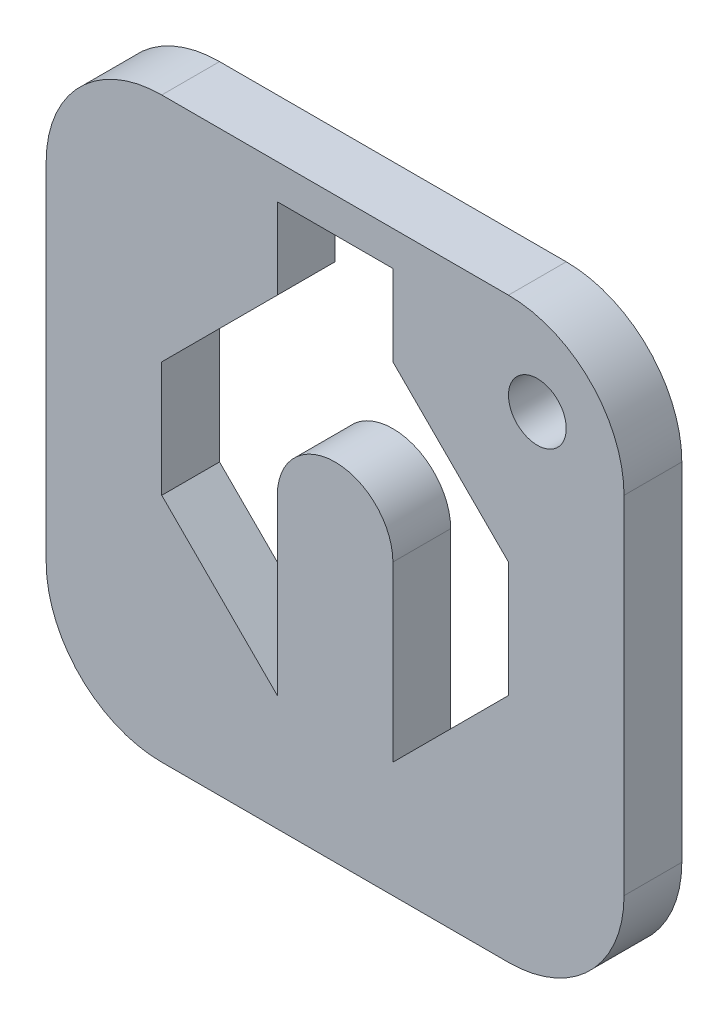
SolidWorks part; units mm, degrees
ref_plane "Z Plane" through (0, 0, 0) normal (0, 0, 1) x (1, 0, 0)
ref_plane "Y Plane" through (0, 0, 0) normal (0, 1, 0) x (1, 0, 0)
ref_plane "X Plane" through (0, 0, 0) normal (1, 0, 0) x (0, 0, -1)
sketch "Sketch2" plane through (0, 0, 0) normal (0, 0, 1) x (1, 0, 0)
  line L1 (-25, 25) -> (25, 25)
  line L2 (-25, 25) -> (-25, -25)
  line L3 (-25, -25) -> (25, -25)
  line L4 (25, 25) -> (25, -25)
  dimension "D1" = 50
  dimension "D2" = 50
  dimension "D3" = 25
  dimension "D4" = 25
extrude "Boss-Extrude1" add sketch "Sketch2" along normal blind 5
fillet "Fillet1" radius 10 4 edges at (-25, -25, 2.5) (25, 25, 2.5) (25, -25, 2.5) (-25, 25, 2.5)
sketch "Sketch3" plane through (0, 0, 5) normal (0, 0, 1) x (1, 0, 0)
  line L0 (-5, 0) -> (-5, -15)
  line L1 (-5, -15) -> (-15, -5)
  line L2 (-15, -5) -> (-15, 5)
  line L3 (-15, 5) -> (-5, 15)
  line L4 (-5, 15) -> (-5, 22)
  line L5 (-5, 22) -> (5, 22)
  line L6 (5, 22) -> (5, 15)
  line L7 (5, 15) -> (15, 5)
  line L8 (15, 5) -> (15, -5)
  line L9 (15, -5) -> (5, -15)
  line L10 (5, -15) -> (5, 0)
  line L11 (15, 25) -> (-15, 25) construction
  line L12 (-25, 15) -> (-25, -15) construction
  line L13 (25, -15) -> (25, 15) construction
  line L14 (-15, -25) -> (15, -25) construction
  circle A0 centre (17.5, 17.5) radius 2.5
  arc A2 (-5, 0) -> (5, 0) centre (0, 0) cw
  dimension "D1" = 5
  dimension "D2" = 3
  dimension "D3" = 10
  dimension "D4" = 10
  dimension "D5" = 10
  dimension "D6" = 10
  dimension "D7" = 45
  dimension "D8" = 10
  dimension "D9" = 10
  dimension "D10" = 10
  dimension "D11" = 7.5
  dimension "D12" = 7.5
  dimension "D13" = 25
extrude "Cut-Extrude1" cut sketch "Sketch3" against normal through all
equation "\"D2@Sketch2\"=\"D1@Sketch2\""
equation "\"D3@Sketch2\"=\"D1@Sketch2\"/2"
equation "\"D4@Sketch2\"=\"D2@Sketch2\"/2"
equation "\"D12@Sketch3\"=\"D11@Sketch3\""
